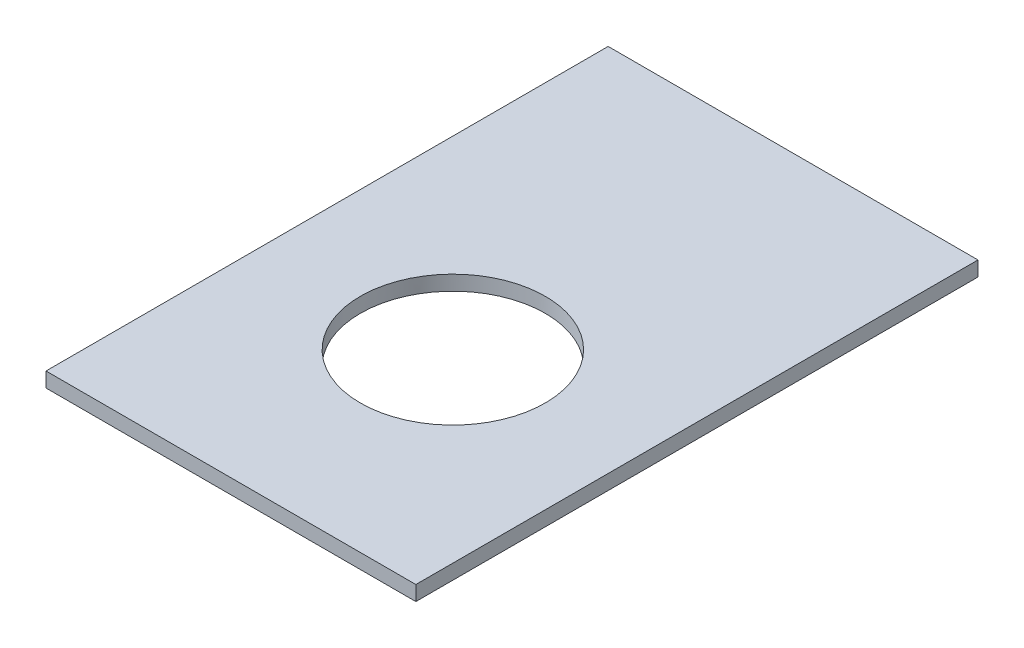
SolidWorks part; units mm, degrees
ref_plane "Ön Düzlem" through (0, 0, 0) normal (0, 0, 1) x (1, 0, 0)
ref_plane "Üst Düzlem" through (0, 0, 0) normal (0, 1, 0) x (1, 0, 0)
ref_plane "Sağ Düzlem" through (0, 0, 0) normal (1, 0, 0) x (0, 0, -1)
sketch "Sketch1" plane through (0, 0, 0) normal (0, 1, 0) x (1, 0, 0)
  line L1 (-250, -380) -> (250, -380)
  line L2 (-250, -380) -> (-250, 380)
  line L3 (-250, 380) -> (250, 380)
  line L4 (250, -380) -> (250, 380)
  line L5 (-250, -380) -> (250, 380) construction
  line L6 (-250, 380) -> (250, -380) construction
  point P0 (0, 0)
  dimension "D1" = 500
  dimension "D2" = 760
extrude "Boss-Extrude1" add sketch "Sketch1" along normal blind 20
sketch "Sketch3" plane through (0, 20, 0) normal (0, 1, 0) x (1, 0, 0)
  line L0 (-250, -380) -> (250, -380) construction
  line L1 (250, -380) -> (250, 380) construction
  circle A0 centre (0, -80) radius 125
  dimension "D1" = 250
  dimension "D2" = 300
  dimension "D3" = 250
extrude "Cut-Extrude2" cut sketch "Sketch3" against normal up to next
